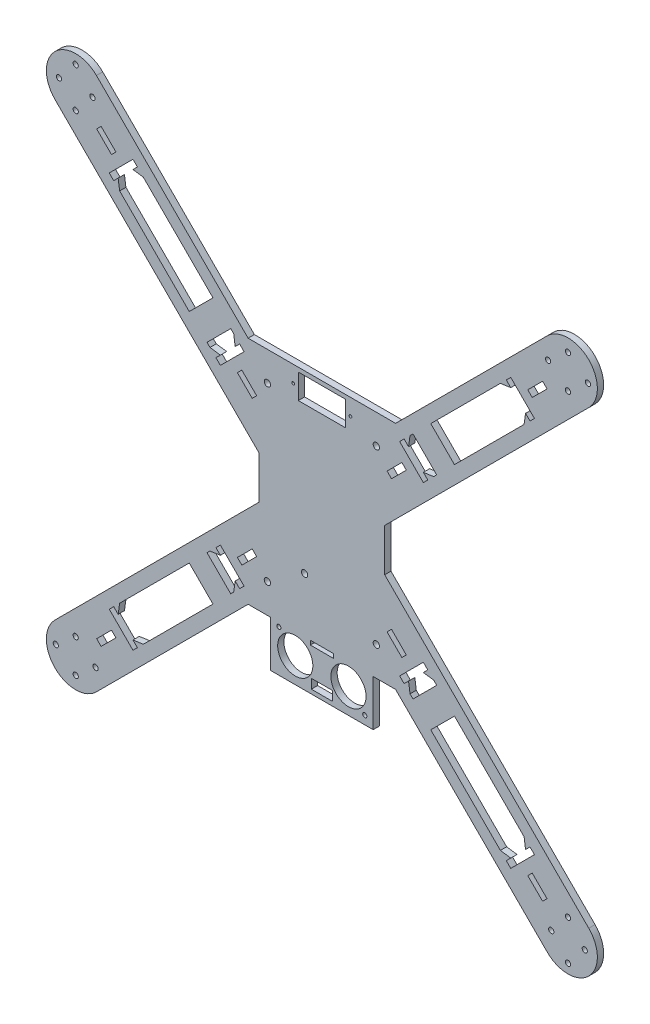
SolidWorks part; units mm, degrees
material "Custom Plastic"
ref_plane "Front Plane" through (0, 0, 0) normal (0, 0, 1) x (1, 0, 0)
ref_plane "Top Plane" through (0, 0, 0) normal (0, 1, 0) x (1, 0, 0)
ref_plane "Right Plane" through (0, 0, 0) normal (1, 0, 0) x (0, 0, -1)
sketch "Sketch1" plane through (0, 0, 0) normal (0, 0, 1) x (1, 0, 0)
  line L0 (117.5, 117.5) -> (-117.5, 117.5) construction
  line L1 (-117.5, 117.5) -> (117.5, -117.5) construction
  line L2 (117.5, -117.5) -> (-117.5, -117.5) construction
  line L3 (-117.5, -117.5) -> (117.5, 117.5) construction
  line L4 (117.5, 117.5) -> (117.5, -117.5) construction
  line L5 (-117.5, 117.5) -> (-117.5, -117.5) construction
  line L6 (0, 117.5) -> (0, -117.5) construction
  line L7 (35.201, 55) -> (-35.201, 55)
  line L8 (-30, 55) -> (30, 55) construction
  line L9 (-35.201, 55) -> (-107.6005, 127.3995)
  line L10 (-127.3995, 107.6005) -> (-30, 10.201)
  line L11 (-117.5, 0) -> (117.5, 0) construction
  line L12 (-30, 10.201) -> (-30, -10.201)
  line L13 (30, 55) -> (30, -55) construction
  line L14 (30, -55) -> (-30, -55) construction
  line L15 (-30, -55) -> (-30, 55) construction
  line L16 (30, 55) -> (-30, -55) construction
  line L17 (-24.5, -55) -> (-24.5, -77)
  line L18 (-127.3995, -107.6005) -> (-30, -10.201)
  line L19 (-24.5, -77) -> (24.5, -77)
  line L20 (-35.201, -55) -> (-107.6005, -127.3995)
  line L21 (35.201, -55) -> (24.5, -55)
  line L22 (35.201, -55) -> (107.6005, -127.3995)
  line L23 (127.3995, -107.6005) -> (30, -10.201)
  line L24 (30, 10.201) -> (30, -10.201)
  line L25 (127.3995, 107.6005) -> (30, 10.201)
  line L26 (35.201, 55) -> (107.6005, 127.3995)
  line L27 (24.5, -55) -> (24.5, -77)
  line L28 (-24.5, -55) -> (-35.201, -55)
  arc A0 (-107.6005, 127.3995) -> (-127.3995, 107.6005) centre (-117.5, 117.5) ccw
  arc A12 (-107.6005, -127.3995) -> (-127.3995, -107.6005) centre (-117.5, -117.5) cw
  arc A16 (107.6005, -127.3995) -> (127.3995, -107.6005) centre (117.5, -117.5) ccw
  arc A24 (107.6005, 127.3995) -> (127.3995, 107.6005) centre (117.5, 117.5) cw
  point P3 (0, 0)
  point P18 (0, 0)
  point P21 (0, -77)
  point P33 (-117.5, 117.5)
  point P34 (-30, 0)
  point P65 (0, -55)
  point P80 (0, 55)
  dimension "D3" = 14
  dimension "D8" = 24.5
  dimension "D7" = 22
  dimension "D1" = 235
  dimension "D2" = 235
  dimension "D4" = 60
  dimension "D5" = 110
  dimension "D6" = 28
extrude "Boss-Extrude1" add sketch "Sketch1" against normal blind 3
sketch "Sketch4" plane through (0, 0, 0) normal (0, 0, 1) x (1, 0, 0)
  line L0 (0, 0) -> (0, 55) construction
  line L1 (35.201, 55) -> (-35.201, 55) construction
  line L2 (0, 0) -> (-30, 0) construction
  line L3 (-30, 10.201) -> (-30, -10.201) construction
  line L4 (-30, 0) -> (-30, 10.201) construction
  line L5 (-30, 10.201) -> (-127.3995, 107.6005) construction
  line L6 (-35.201, 55) -> (-107.6005, 127.3995) construction
  line L7 (-107.6005, 127.3995) -> (-127.3995, 107.6005) construction
  line L8 (-117.5, 127) -> (-117.5, 108) construction
  line L9 (-125.5, 117.5) -> (-109.5, 117.5) construction
  circle A4 centre (-26, 41) radius 1.5
  circle A9 centre (-26, -41) radius 1.5
  circle A18 centre (26, -41) radius 1.5
  circle A19 centre (26, 41) radius 1.5
  circle A20 centre (-117.5, 127) radius 1.25
  circle A21 centre (-117.5, 108) radius 1.25
  circle A22 centre (-125.5, 117.5) radius 1.25
  circle A23 centre (-109.5, 117.5) radius 1.25
  circle A24 centre (117.5, 109.5) radius 1.25
  circle A25 centre (108, 117.5) radius 1.25
  circle A26 centre (117.5, 125.5) radius 1.25
  circle A27 centre (127, 117.5) radius 1.25
  circle A28 centre (109.5, -117.5) radius 1.25
  circle A29 centre (117.5, -108) radius 1.25
  circle A30 centre (125.5, -117.5) radius 1.25
  circle A31 centre (117.5, -127) radius 1.25
  circle A32 centre (-117.5, -109.5) radius 1.25
  circle A33 centre (-108, -117.5) radius 1.25
  circle A34 centre (-117.5, -125.5) radius 1.25
  circle A35 centre (-127, -117.5) radius 1.25
  point P16 (-117.5, 117.5)
  point P19 (-117.5, 117.5)
  point P26 (-117.5, 117.5)
  point P62 (0, 0)
  dimension "D1" = 45
  dimension "D6" = 3
  dimension "D4" = 2.5
  dimension "D2" = 19
  dimension "D7" = 14
  dimension "D8" = 4
  dimension "D3" = 16
extrude "Cut-Extrude1" cut sketch "Sketch4" against normal blind 3
sketch "Sketch5" plane through (0, 0, 0) normal (0, 0, 1) x (1, 0, 0)
  line L7 (-11.25, 53) -> (-11.25, 41.2)
  line L8 (-11.25, 41.2) -> (11.25, 41.2)
  line L9 (11.25, 41.2) -> (11.25, 53)
  line L10 (11.25, 53) -> (-11.25, 53)
  line L12 (0, 53) -> (0, 41.2) construction
  line L13 (-13.65, 47.1) -> (13.65, 47.1) construction
  line L14 (35.201, 55) -> (-35.201, 55) construction
  circle A2 centre (-13.65, 47.1) radius 0.65
  circle A3 centre (13.65, 47.1) radius 0.65
  point P20 (0, 47.1)
  point P21 (0, 47.1)
  point P26 (0, 55)
  dimension "D8" = 1.3
  dimension "D9" = 1.3
  dimension "D10" = 27.3
  dimension "D11" = 22.5
  dimension "D12" = 11.8
  dimension "D13" = 2
extrude "Cut-Extrude2" cut sketch "Sketch5" against normal blind 3
sketch "Sketch6" plane through (0, 0, 0) normal (0, 0, 1) x (1, 0, 0)
  line L1 (-11.25, 41.2) -> (11.25, 41.2) construction
  circle A0 centre (-8.25, -28.8) radius 1.5
  dimension "D3" = 3
  dimension "D1" = 70
  dimension "D2" = 3
extrude "Cut-Extrude3" cut sketch "Sketch6" against normal blind 3
sketch "Sketch7" plane through (0, 0, 0) normal (0, 0, 1) x (1, 0, 0)
  line L0 (-22.5, -55) -> (-22.5, -75) construction
  line L5 (-22.5, -75) -> (22.5, -75) construction
  line L6 (22.5, -75) -> (22.5, -55) construction
  line L7 (22.5, -55) -> (-22.5, -55) construction
  line L8 (0, -55) -> (0, -75) construction
  line L9 (-12.7, -65) -> (0, -65) construction
  line L10 (-24.5, -77) -> (24.5, -77) construction
  line L11 (-24.5, -55) -> (-24.5, -77) construction
  line L12 (-5.5, -55) -> (-5.5, -57)
  line L13 (-5.5, -57) -> (5.5, -57)
  line L15 (5.5, -55) -> (-5.5, -55)
  line L16 (-5, -75) -> (-5, -70.5)
  line L17 (-5, -70.5) -> (5, -70.5)
  line L21 (5, -75) -> (-5, -75)
  line L22 (5.5, -55) -> (5.5, -57)
  line L23 (5, -75) -> (5, -70.5)
  circle A5 centre (-20.5, -57) radius 1
  circle A6 centre (-12.7, -65) radius 8.4
  circle A7 centre (12.7, -65) radius 8.4
  circle A8 centre (20.5, -73) radius 1
  point P25 (0, -57)
  point P26 (0, -70.5)
  dimension "D3" = 2
  dimension "D6" = 20
  dimension "D13" = 5
  dimension "D5" = 45
  dimension "D1" = 2
  dimension "D4" = 16.8
  dimension "D14" = 2
  dimension "D2" = 2
  dimension "D7" = 2
  dimension "D8" = 2
  dimension "D9" = 12.7
  dimension "D10" = 5.5
  dimension "D11" = 2
  dimension "D12" = 4.5
  dimension "D15" = 2
  dimension "D16" = 2
extrude "Cut-Extrude4" cut sketch "Sketch7" against normal blind 3
sketch "Sketch8" plane through (0, 0, 0) normal (0, 0, 1) x (1, 0, 0)
  line L0 (101.4792, -90.1655) -> (90.1655, -101.4792)
  line L1 (90.1655, -101.4792) -> (88.0442, -99.3579)
  line L2 (37.1325, -48.4462) -> (48.4462, -37.1325)
  line L3 (48.4462, -37.1325) -> (50.5675, -39.2538)
  line L4 (105.7218, -85.9228) -> (85.9228, -105.7218) construction
  line L5 (127.3995, -107.6005) -> (30, -10.201) construction
  line L6 (35.201, -55) -> (107.6005, -127.3995) construction
  line L7 (40.3144, -38.1931) -> (38.1931, -40.3144)
  line L8 (117.5, -109.5) -> (109.5, -117.5) construction
  line L9 (38.1931, -40.3144) -> (31.1221, -33.2434)
  line L10 (50.5675, 39.2538) -> (48.4462, 37.1325)
  line L11 (31.1221, -33.2434) -> (33.2434, -31.1221)
  line L12 (33.2434, -31.1221) -> (40.3144, -38.1931)
  line L13 (42.7893, -42.7893) -> (39.2538, -39.2538) construction
  line L14 (35.201, -55) -> (107.6005, -127.3995) construction
  line L15 (100.4185, -98.2972) -> (98.2972, -100.4185)
  line L16 (98.2972, -100.4185) -> (105.3683, -107.4896)
  line L17 (105.3683, -107.4896) -> (107.4896, -105.3683)
  line L18 (107.4896, -105.3683) -> (100.4185, -98.2972)
  line L19 (99.3579, -99.3579) -> (95.8223, -95.8223) construction
  line L20 (-101.4792, -90.1655) -> (-99.3579, -88.0442)
  line L21 (-100.4185, -98.2972) -> (-107.4896, -105.3683)
  line L22 (-107.4896, -105.3683) -> (-105.3683, -107.4896)
  line L23 (-105.3683, -107.4896) -> (-98.2972, -100.4185)
  line L24 (-98.2972, -100.4185) -> (-100.4185, -98.2972)
  line L25 (-90.1655, -101.4792) -> (-101.4792, -90.1655)
  line L26 (-37.1325, -48.4462) -> (-39.2538, -50.5675)
  line L27 (-48.4462, -37.1325) -> (-37.1325, -48.4462)
  line L28 (-38.1931, -40.3144) -> (-40.3144, -38.1931)
  line L29 (-31.1221, -33.2434) -> (-38.1931, -40.3144)
  line L30 (-40.3144, -38.1931) -> (-33.2434, -31.1221)
  line L31 (-33.2434, -31.1221) -> (-31.1221, -33.2434)
  line L32 (-90.1655, 101.4792) -> (-88.0442, 99.3579)
  line L33 (-98.2972, 100.4185) -> (-105.3683, 107.4896)
  line L34 (-105.3683, 107.4896) -> (-107.4896, 105.3683)
  line L35 (-107.4896, 105.3683) -> (-100.4185, 98.2972)
  line L36 (-100.4185, 98.2972) -> (-98.2972, 100.4185)
  line L37 (-101.4792, 90.1655) -> (-90.1655, 101.4792)
  line L38 (-48.4462, 37.1325) -> (-50.5675, 39.2538)
  line L39 (-37.1325, 48.4462) -> (-48.4462, 37.1325)
  line L40 (-40.3144, 38.1931) -> (-38.1931, 40.3144)
  line L41 (-33.2434, 31.1221) -> (-40.3144, 38.1931)
  line L42 (-38.1931, 40.3144) -> (-31.1221, 33.2434)
  line L43 (-31.1221, 33.2434) -> (-33.2434, 31.1221)
  line L44 (101.4792, 90.1655) -> (99.3579, 88.0442)
  line L45 (100.4185, 98.2972) -> (107.4896, 105.3683)
  line L46 (107.4896, 105.3683) -> (105.3683, 107.4896)
  line L47 (105.3683, 107.4896) -> (98.2972, 100.4185)
  line L48 (98.2972, 100.4185) -> (100.4185, 98.2972)
  line L49 (90.1655, 101.4792) -> (101.4792, 90.1655)
  line L50 (37.1325, 48.4462) -> (39.2538, 50.5675)
  line L51 (48.4462, 37.1325) -> (37.1325, 48.4462)
  line L52 (38.1931, 40.3144) -> (40.3144, 38.1931)
  line L53 (31.1221, 33.2434) -> (38.1931, 40.3144)
  line L54 (40.3144, 38.1931) -> (33.2434, 31.1221)
  line L55 (33.2434, 31.1221) -> (31.1221, 33.2434)
  line L56 (30, 10.201) -> (127.3995, 107.6005) construction
  line L57 (42.0822, 53.3959) -> (85.2157, 96.5294)
  line L58 (96.5294, 85.2157) -> (53.3959, 42.0822)
  line L59 (88.0442, 99.3579) -> (90.1655, 101.4792)
  line L60 (99.3579, -88.0442) -> (97.2365, -90.1655)
  line L61 (-96.5294, -85.2157) -> (-53.3959, -42.0822)
  line L62 (97.2365, -90.1655) -> (96.5294, -85.2157)
  line L63 (99.3579, -88.0442) -> (101.4792, -90.1655)
  line L64 (88.0442, -99.3579) -> (90.1655, -97.2365)
  line L65 (-88.0442, -99.3579) -> (-90.1655, -101.4792)
  line L66 (90.1655, -97.2365) -> (85.2157, -96.5294)
  line L67 (85.2157, -96.5294) -> (42.0822, -53.3959)
  line L68 (50.5675, -39.2538) -> (48.4462, -41.3751)
  line L69 (48.4462, -41.3751) -> (53.3959, -42.0822)
  line L70 (53.3959, -42.0822) -> (96.5294, -85.2157)
  line L71 (39.2538, -50.5675) -> (41.3751, -48.4462)
  line L72 (41.3751, -48.4462) -> (42.0822, -53.3959)
  line L73 (39.2538, -50.5675) -> (37.1325, -48.4462)
  line L74 (-90.1655, -97.2365) -> (-85.2157, -96.5294)
  line L75 (-88.0442, -99.3579) -> (-90.1655, -97.2365)
  line L76 (-97.2365, -90.1655) -> (-96.5294, -85.2157)
  line L77 (-99.3579, -88.0442) -> (-97.2365, -90.1655)
  line L78 (-41.3751, -48.4462) -> (-42.0822, -53.3959)
  line L79 (-39.2538, -50.5675) -> (-41.3751, -48.4462)
  line L80 (-48.4462, -41.3751) -> (-53.3959, -42.0822)
  line L81 (-50.5675, -39.2538) -> (-48.4462, -41.3751)
  line L82 (-97.2365, 90.1655) -> (-96.5294, 85.2157)
  line L83 (-99.3579, 88.0442) -> (-97.2365, 90.1655)
  line L84 (-90.1655, 97.2365) -> (-85.2157, 96.5294)
  line L85 (-88.0442, 99.3579) -> (-90.1655, 97.2365)
  line L86 (-48.4462, 41.3751) -> (-53.3959, 42.0822)
  line L87 (-50.5675, 39.2538) -> (-48.4462, 41.3751)
  line L88 (-41.3751, 48.4462) -> (-42.0822, 53.3959)
  line L89 (-39.2538, 50.5675) -> (-41.3751, 48.4462)
  line L90 (90.1655, 97.2365) -> (85.2157, 96.5294)
  line L91 (88.0442, 99.3579) -> (90.1655, 97.2365)
  line L92 (97.2365, 90.1655) -> (96.5294, 85.2157)
  line L93 (99.3579, 88.0442) -> (97.2365, 90.1655)
  line L94 (41.3751, 48.4462) -> (42.0822, 53.3959)
  line L95 (39.2538, 50.5675) -> (41.3751, 48.4462)
  line L96 (48.4462, 41.3751) -> (53.3959, 42.0822)
  line L97 (50.5675, 39.2538) -> (48.4462, 41.3751)
  line L98 (-39.2538, 50.5675) -> (-37.1325, 48.4462)
  line L99 (-53.3959, 42.0822) -> (-96.5294, 85.2157)
  line L100 (-99.3579, 88.0442) -> (-101.4792, 90.1655)
  line L101 (-85.2157, 96.5294) -> (-42.0822, 53.3959)
  line L102 (-42.0822, -53.3959) -> (-85.2157, -96.5294)
  line L103 (-50.5675, -39.2538) -> (-48.4462, -37.1325)
  point P10 (95.8223, -95.8223)
  point P11 (95.8223, -95.8223)
  point P68 (0, 0)
  point P122 (0, 0)
  dimension "D1" = 25
  dimension "D2" = 75
  dimension "D3" = 3
  dimension "D4" = 10
  dimension "D5" = 5
  dimension "D6" = 6
  dimension "D7" = 3
  dimension "D8" = 10
  dimension "D9" = 5
  dimension "D11" = 6
  dimension "D12" = 3
  dimension "D13" = 4
  dimension "D14" = 3
  dimension "D15" = 3
  dimension "D16" = 4
  dimension "D17" = 3
  dimension "D18" = 3
  dimension "D19" = 4
  dimension "D20" = 3
  dimension "D21" = 3
  dimension "D22" = 4
  dimension "D23" = 3
  dimension "D10" = 4
extrude "Cut-Extrude5" cut sketch "Sketch8" against normal through all
sketch "Sketch9" plane through (-5.6569, 5.6569, 0) normal (0.7071, -0.7071, 0) x (0, 0, -1)
  line L0 (3, 128.5132) -> (3, 67.5132) construction
  line L1 (3, 81.5132) -> (0, 81.5132)
  line L2 (3, 81.5132) -> (3, 69.5132)
  line L3 (3, 69.5132) -> (0, 69.5132)
  line L4 (0, 81.5132) -> (0, 69.5132)
  line L5 (0, 128.5132) -> (0, 67.5132) construction
  line L6 (0, 0) -> (28.0274, 0) construction
  line L7 (3, 63.5132) -> (0, 63.5132) construction
  dimension "D1" = 6
  dimension "D2" = 12
extrude "Boss-Extrude2" add sketch "Sketch9" along normal up to next
sketch "Sketch11" plane through (5.6569, 5.6569, 0) normal (-0.7071, -0.7071, 0) x (0, 0, 1)
  line L0 (-3, -128.5132) -> (-3, -67.5132) construction
  line L1 (-3, -69.5132) -> (0, -69.5132)
  line L2 (-3, -69.5132) -> (-3, -81.5132)
  line L3 (-3, -81.5132) -> (0, -81.5132)
  line L4 (0, -69.5132) -> (0, -81.5132)
  line L5 (0, -128.5132) -> (0, -67.5132) construction
  line L6 (-3, -63.5132) -> (0, -63.5132) construction
  dimension "D1" = 6
  dimension "D2" = 12
extrude "Boss-Extrude3" add sketch "Sketch11" along normal up to next
sketch "Sketch12" plane through (5.6569, -5.6569, 0) normal (-0.7071, 0.7071, 0) x (0, 0, 1)
  line L0 (-3, -128.5132) -> (-3, -67.5132) construction
  line L1 (-3, -69.5132) -> (0, -69.5132)
  line L2 (-3, -69.5132) -> (-3, -81.5132)
  line L3 (-3, -81.5132) -> (0, -81.5132)
  line L4 (0, -69.5132) -> (0, -81.5132)
  line L5 (0, -128.5132) -> (0, -67.5132) construction
  dimension "D1" = 6
  dimension "D2" = 12
extrude "Boss-Extrude4" add sketch "Sketch12" along normal up to next
sketch "Sketch13" plane through (5.6569, 5.6569, 0) normal (-0.7071, -0.7071, 0) x (0, 0, 1)
  line L0 (-3, 67.5132) -> (-3, 128.5132) construction
  line L1 (-3, 69.5132) -> (0, 69.5132)
  line L2 (-3, 69.5132) -> (-3, 81.5132)
  line L3 (-3, 81.5132) -> (0, 81.5132)
  line L4 (0, 69.5132) -> (0, 81.5132)
  line L5 (0, 67.5132) -> (0, 128.5132) construction
  dimension "D1" = 6
  dimension "D2" = 12
extrude "Boss-Extrude5" add sketch "Sketch13" along normal up to next
